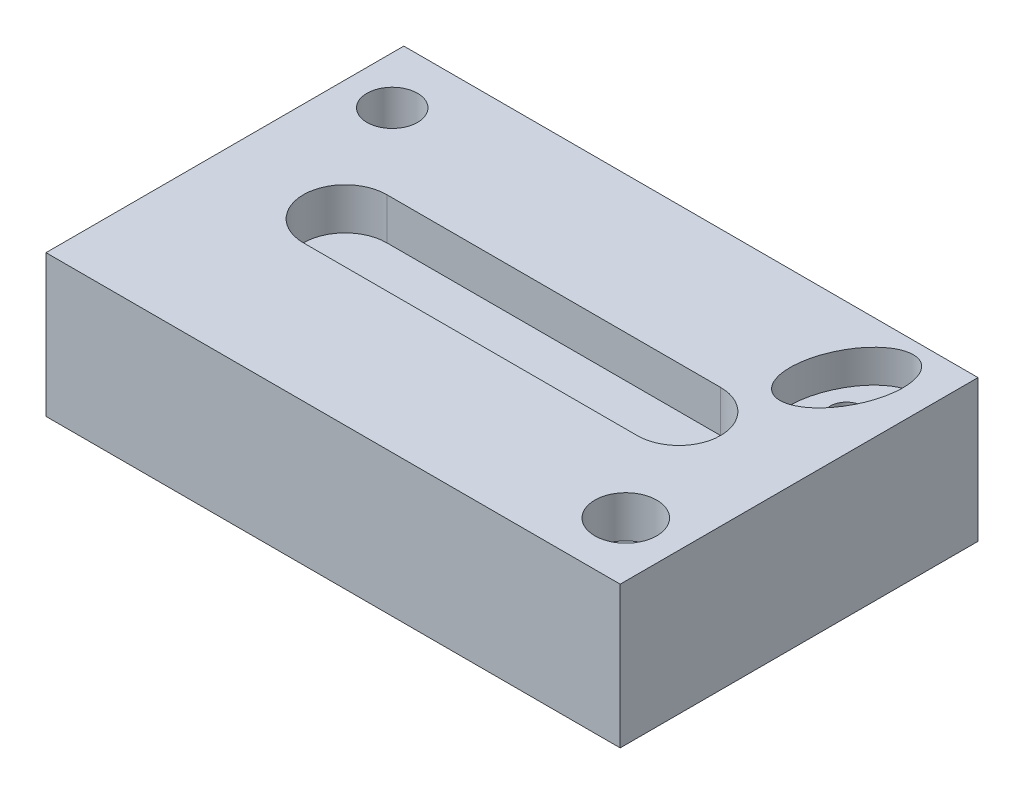
SolidWorks part; units mm, degrees
ref_plane "Front Plane" through (0, 0, 0) normal (0, 0, 1) x (1, 0, 0)
ref_plane "Top Plane" through (0, 0, 0) normal (0, 1, 0) x (1, 0, 0)
ref_plane "Right Plane" through (0, 0, 0) normal (1, 0, 0) x (0, 0, -1)
sketch "Sketch1" plane through (0, 0, 0) normal (0, 1, 0) x (1, 0, 0)
  line L1 (-87.3981, -54.4636) -> (87.3981, -54.4636)
  line L2 (-87.3981, -54.4636) -> (-87.3981, 54.4636)
  line L3 (-87.3981, 54.4636) -> (87.3981, 54.4636)
  line L4 (87.3981, -54.4636) -> (87.3981, 54.4636)
  line L5 (-87.3981, -54.4636) -> (87.3981, 54.4636) construction
  line L6 (-87.3981, 54.4636) -> (87.3981, -54.4636) construction
  point P0 (0, 0)
extrude "Boss-Extrude1" add sketch "Sketch1" along normal blind 43.18
sketch "Sketch2" plane through (0, 43.18, 0) normal (0, 1, 0) x (1, 0, 0)
  line L0 (-50.8, 0) -> (50.8, 0) construction
  line L1 (-50.8, 12.7) -> (50.8, 12.7)
  line L2 (-50.8, -12.7) -> (50.8, -12.7)
  arc A0 (-50.8, 12.7) -> (-50.8, -12.7) centre (-50.8, 0) ccw
  arc A1 (50.8, -12.7) -> (50.8, 12.7) centre (50.8, 0) ccw
  circle A2 centre (-72.874, 36.4086) radius 7.6974
  circle A3 centre (70.8013, -36.1578) radius 9.4308
  point P2 (0, 0)
  dimension "D2" = 101.6
  dimension "D1" = 25.4
extrude "Cut-Extrude1" cut sketch "Sketch2" against normal blind 12.7
sketch "Sketch3" plane through (0, 43.18, 0) normal (0, 1, 0) x (1, 0, 0)
  line L1 (87.3981, -54.4636) -> (87.3981, 54.4636) construction
  line L2 (87.3981, 54.4636) -> (-87.3981, 54.4636) construction
  ellipse E0 centre (67.3981, 34.4636) end of major axis (73.8505, 50.1915) minor radius 10
  point P1 (0, 0)
  point P8 (0, 0)
  point P11 (0, 0)
  dimension "D1" = 20
  dimension "D2" = 20
extrude "Cut-Extrude2" cut sketch "Sketch3" against normal blind 10
sketch "Sketch4" plane through (0, 33.18, 0) normal (0, 1, 0) x (1, 0, 0)
  line L0 (87.3981, -54.4636) -> (87.3981, 54.4636) construction
  line L2 (87.3981, 54.4636) -> (-87.3981, 54.4636) construction
  circle A0 centre (67.3981, 34.4636) radius 5
  point P6 (56.9928, 54.4636)
  dimension "D1" = 10
  dimension "D2" = 20
  dimension "D3" = 20
extrude "Cut-Extrude3" cut sketch "Sketch4" against normal blind 50 from offset 0
